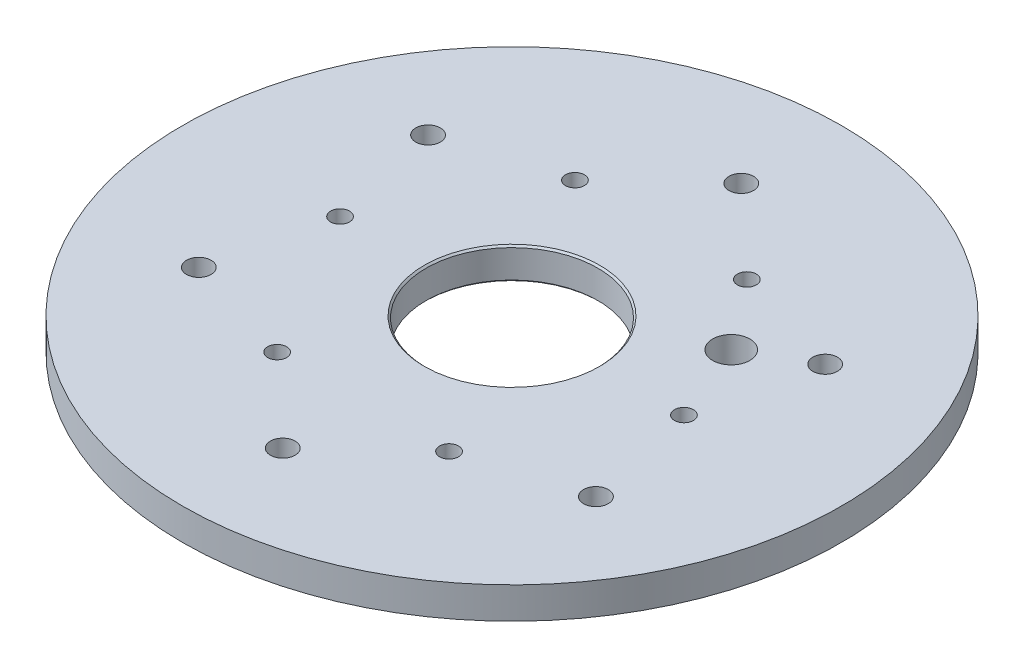
SolidWorks part; units mm, degrees
ref_plane "Front Plane" through (0, 0, 0) normal (0, 0, 1) x (1, 0, 0)
ref_plane "Top Plane" through (0, 0, 0) normal (0, 1, 0) x (1, 0, 0)
ref_plane "Right Plane" through (0, 0, 0) normal (1, 0, 0) x (0, 0, -1)
sketch "Sketch1" plane through (0, 0, 0) normal (0, 1, 0) x (1, 0, 0)
  line L1 (0, 0) -> (-30, 0) construction
  line L2 (0, 0) -> (-34.641, 20) construction
  circle A0 centre (0, 0) radius 57.5
  circle A2 centre (-30, 0) radius 1.65
  circle A3 centre (-15, 25.9808) radius 1.65
  circle A4 centre (15, 25.9808) radius 1.65
  circle A5 centre (30, 0) radius 1.65
  circle A6 centre (15, -25.9808) radius 1.65
  circle A7 centre (-15, -25.9808) radius 1.65
  circle A8 centre (-34.641, 20) radius 2.15
  circle A9 centre (0, 40) radius 2.15
  circle A10 centre (34.641, 20) radius 2.15
  circle A11 centre (34.641, -20) radius 2.15
  circle A12 centre (0, -40) radius 2.15
  circle A13 centre (-34.641, -20) radius 2.15
  circle A14 centre (0, 0) radius 15
  point P8 (0, 0)
  dimension "D2" = 3.3
  dimension "D3" = 115
  dimension "D7" = 4.3
  dimension "D9" = 30
  dimension "D1" = 30
  dimension "D4" = 30
  dimension "D6" = 40
  dimension "D5" = 6
  dimension "D8" = 6
extrude "Boss-Extrude1" add sketch "Sketch1" along normal blind 5.5
chamfer "Chamfer2" distance 0.3 angle 45 2 edges at (0, 0, 15) (0, 5.5, 15)
sketch "Sketch3" plane through (0, 0, 0) normal (0, -1, 0) x (1, 0, 0)
  line L0 (0, 0) -> (24.2487, -14) construction
  line L1 (24.2487, -14) -> (34.641, -20) construction
  circle A0 centre (24.2487, -14) radius 3.25
  dimension "D2" = 6.5
  dimension "D1" = 28
extrude "Cut-Extrude2" cut sketch "Sketch3" against normal blind 10
